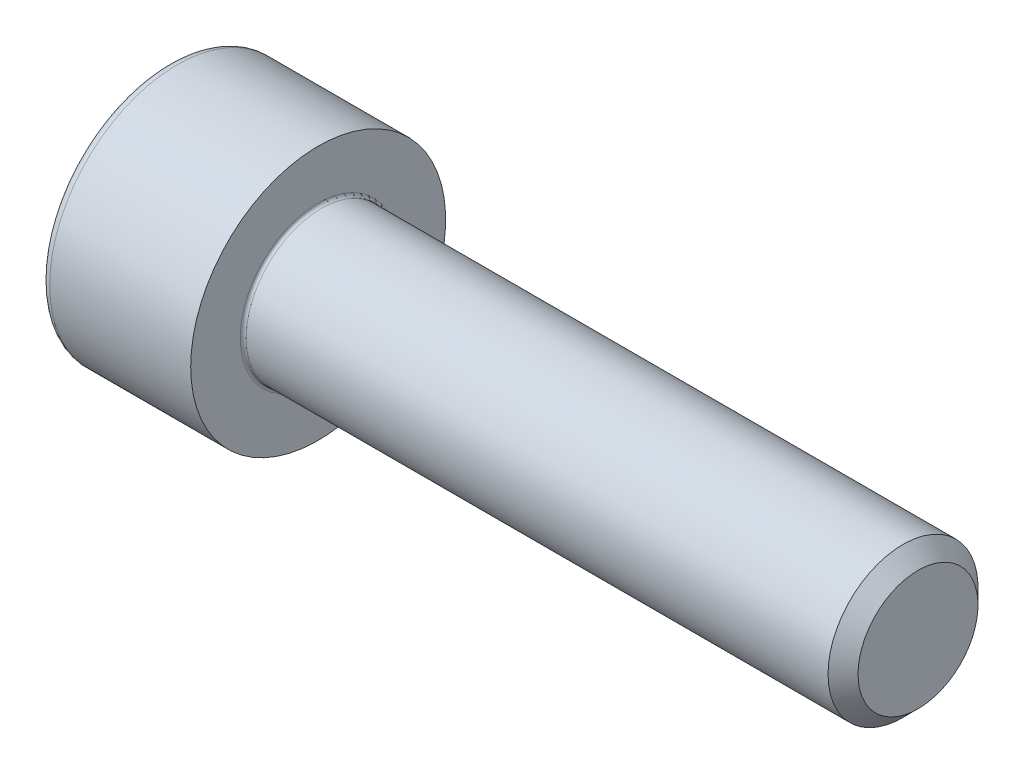
SolidWorks part; units mm, degrees
revolve "Base-Revolve" add sketch "BodySke"
sketch "BodySke" plane through (0, 0, 0) normal (0, 0, 1) x (1, 0, 0)
  line L0 (0, 0) -> (0, 4.25)
  line L1 (0, 4.25) -> (5, 4.25)
  line L2 (5, 4.25) -> (5, 2.5)
  line L3 (5, 2.5) -> (24.5, 2.5)
  line L4 (25, 2) -> (25, 0)
  line L5 (25, 0) -> (0, 0)
  line L6 (-31.75, 0) -> (127, 0) construction
  line L8 (25, 2) -> (24.5, 2.5)
  line L10 (25, -2) -> (24.5, -2.5) construction
  line L11 (5.5, 9.525) -> (5.5, 3.175) construction
  line L12 (15, 9.525) -> (15, 3.175) construction
  line L13 (9.0069, 9.525) -> (9.0069, 3.175) construction
  dimension "Head_ht" = 5
  dimension "Length" = 20
  dimension "Body_ch_ang" = 45
  dimension "Diameter" = 5
  dimension "Minor_dia" = 4
  dimension "Advance" = 0.5
  dimension "Thread_nom" = 10
  dimension "Thread_length" = 15.9931
  dimension "Head_dia" = 8.5
cosmetic thread "ThreadCosmetic" [suppressed]
fillet "Fillet1" radius 0.1 1 edges at (5, 0, 2.5)
fillet "Fillet2" radius 0.3 1 edges at (0, 0, 4.25)
ref_plane "Plane1" through (0, 0, 0) normal (0, 0, 1) x (1, 0, 0)
ref_plane "Plane2" through (0, 0, 0) normal (0, 1, 0) x (1, 0, 0)
ref_plane "Plane3" through (0, 0, 0) normal (1, 0, 0) x (0, 0, -1)
sketch "Sketch2" plane through (0, 0, 0) normal (0, 0, 1) x (1, 0, 0)
  line L0 (0, 2) -> (1.3, 2)
  line L1 (1.3, 2) -> (2.4547, 0)
  line L2 (-31.75, 0) -> (127, 0) construction
  line L3 (2.4547, 0) -> (0, 0)
  line L4 (0, 0) -> (0, 2)
  line L6 (0, 0) -> (47.625, 0) construction
  dimension "D1" = 2
  dimension "D2" = 60
  dimension "Depth" = 1.3
revolve "Hex-PreBroach" cut sketch "Sketch2" angle 360 about L6
sketch "Sketch3" plane through (0, 0, 0) normal (-1, 0, 0) x (0, 0.5, 0.866)
  line L0 (1.1547, 2) -> (-1.1547, 2)
  line L1 (-1.1547, 2) -> (-2.3094, 0)
  line L2 (1.1547, 2) -> (2.3094, 0)
  line L3 (1.1547, -2) -> (2.3094, 0)
  line L4 (1.1547, -2) -> (-1.1547, -2)
  line L5 (-1.1547, -2) -> (-2.3094, 0)
  dimension "D1" = 2
  dimension "D2" = 2
  dimension "Hex_size" = 4
extrude "Hex" cut sketch "Sketch3" against normal blind 1.3
sketch "ThdSchSke" plane through (0, 0, 0) normal (0, 0, 1) x (1, 0, 0)
  line L0 (15, -2) -> (14.6499, -2.5)
  line L1 (15, -2) -> (15.3501, -2.5)
  line L2 (15.3501, -2.5) -> (15.3501, -3.125)
  line L3 (-3.175, 0) -> (5.1513, 0) construction
  line L4 (0, 3.95) -> (0, -3.95) construction
  line L5 (15.3501, -3.125) -> (14.6499, -3.125)
  line L6 (14.6499, -3.125) -> (14.6499, -2.5)
  dimension "Thread_minor" = 4
  dimension "Diameter" = 5
  dimension "Start" = 15
revolve "ThreadSchematic" [suppressed] cut sketch "ThdSchSke" angle 360 about L3
pattern_linear "ThdSchPat" [suppressed]
equation "\"D2@Sketch3\" = \"Hex_size@Sketch3\" / 2"
equation "\"D1@Sketch3\" = \"Hex_size@Sketch3\" / 2"
equation "\"D1@Sketch2\" = \"Hex_size@Sketch3\" / 2"
equation "\"Thread_minor@ThreadCosmetic\"  =  \"Minor_dia@BodySke\""
equation "\"Depth@Sketch2\" =  \"Key_eng@Hex\""
equation "\"Thread_length@ThreadCosmetic\" = ((sgn( (\"Length@BodySke\" - \"Advance@BodySke\" * 3.0) - \"Thread_nom@BodySke\" )-1)*( (\"Length@BodySke\" - \"Advance@BodySke\" * 3.0) - \"Thread_nom@BodySke\" ))/-2+ \"Thread_nom@BodySke\""
equation "\"Thread_minor@ThdSchSke\" = \"Minor_dia@BodySke\""
equation "\"Diameter@ThdSchSke\" = \"Diameter@BodySke\""
equation "\"Overcut@ThdSchSke\" = \"Diameter@BodySke\" * 1.25"
equation "\"Start@ThdSchSke\" = \"Head_ht@BodySke\" + \"Length@BodySke\" - \"Thread_length@ThreadCosmetic\"  '---Non-countersunk---"
equation "\"Num_threads@ThdSchPat\" = int( \"Thread_length@ThreadCosmetic\" / \"Advance@BodySke\" + 0.999 )  + 1"
equation "\"Advance@ThdSchPat\" = \"Thread_length@ThreadCosmetic\" /  (\"Num_threads@ThdSchPat\" - 1) 'relax it"
equation "\"Num_threads@ThdSchPat\" = \"Num_threads@ThdSchPat\" - sgn( \"Num_threads@ThdSchPat\" - 1) '---chamfered tips only---"
